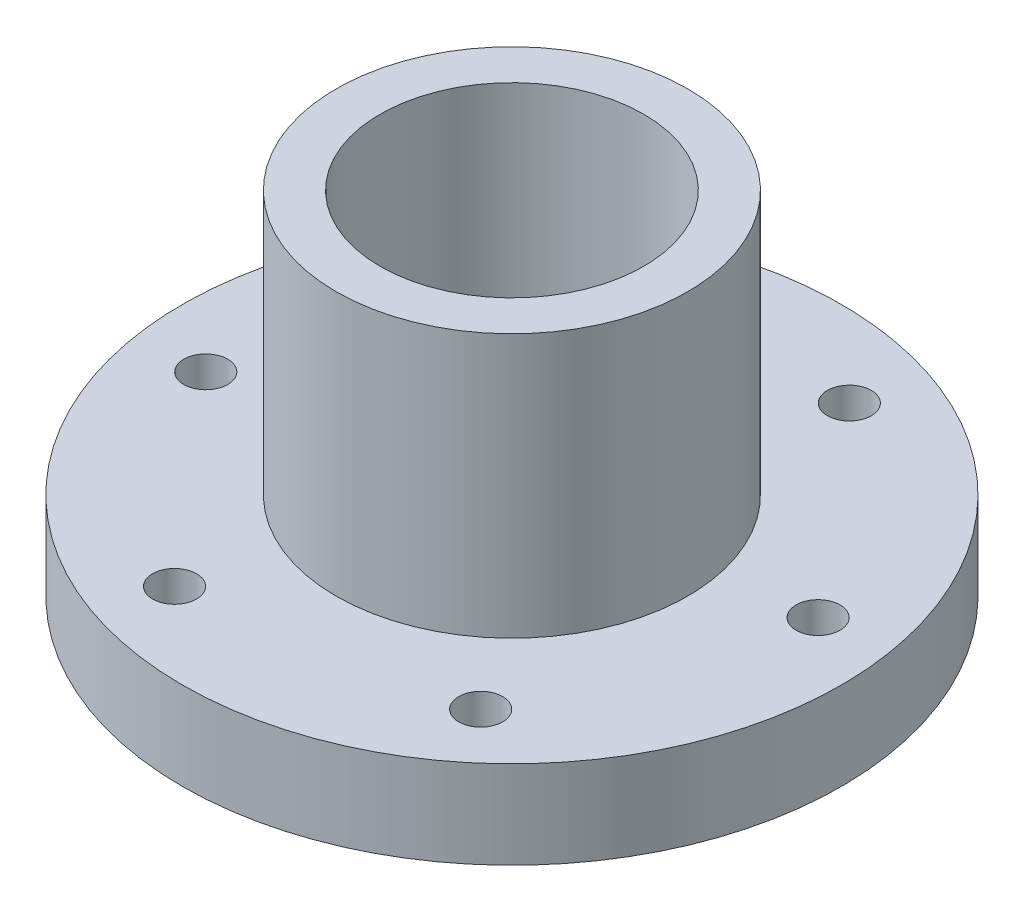
SolidWorks part; units mm, degrees
ref_plane "Front Plane" through (0, 0, 0) normal (0, 0, 1) x (1, 0, 0)
ref_plane "Top Plane" through (0, 0, 0) normal (0, 1, 0) x (1, 0, 0)
ref_plane "Right Plane" through (0, 0, 0) normal (1, 0, 0) x (0, 0, -1)
sketch "Sketch1" plane through (0, 0, 0) normal (0, 0, 1) x (1, 0, 0)
  line L0 (0.1504, -4.8795) -> (-14.1371, -4.8795)
  line L1 (-14.1371, -4.8795) -> (-14.1371, 1.4705)
  line L2 (-14.1371, 1.4705) -> (-3.0246, 1.4705)
  line L3 (-3.0246, 1.4705) -> (-3.0246, 20.5205)
  line L4 (-3.0246, 20.5205) -> (0.1504, 20.5205)
  line L5 (0.1504, 20.5205) -> (0.1504, -4.8795)
  line L7 (9.6754, 1.4705) -> (9.6754, 0) construction
  dimension "D1" = 3.175
  dimension "D2" = 19.05
  dimension "D3" = 12.7
  dimension "D4" = 23.8125
  dimension "D5" = 6.35
revolve "Revolve1" add sketch "Sketch1" angle 360 about L7
hole_wizard "1/8 (0.125) Diameter Hole1" positions "Sketch4" profile "Sketch5" hole size "1/8" standard "ANSI Inch" end condition through all
sketch "Sketch4" plane through (0, 1.4705, 0) normal (0, 1, 0) x (1, 0, 0)
  line L0 (9.6754, 0) -> (1.6073, -22.404) construction
  circle A0 centre (9.6754, 0) radius 23.8125 construction
  circle A1 centre (9.6754, 0) radius 12.7 construction
  point P0 (3.2209, -17.9232)
  point P17 (-9.0738, -3.3719)
  point P18 (-2.6193, 14.5514)
  point P19 (16.1299, 17.9232)
  point P20 (28.4246, 3.3719)
  point P21 (21.9701, -14.5514)
  point P22 (9.6754, 0)
  dimension "D1" = 19.05
  dimension "D2" = 6
sketch "Sketch5" plane through (3.2209, 1.4705, 17.9232) normal (1, 0, 0) x (0, 0, 1)
  line L0 (0, 0) -> (0, 6.35)
  line L1 (0, 6.35) -> (1.5875, 6.35)
  line L2 (1.5875, 6.35) -> (1.5875, 0)
  line L5 (1.5875, 0) -> (0, 0)
  line L11 (0, -6.35) -> (0, 107.95) construction
  dimension "Thru Hole Dia." = 3.175
  dimension "Thru Hole Depth" = 6.35
